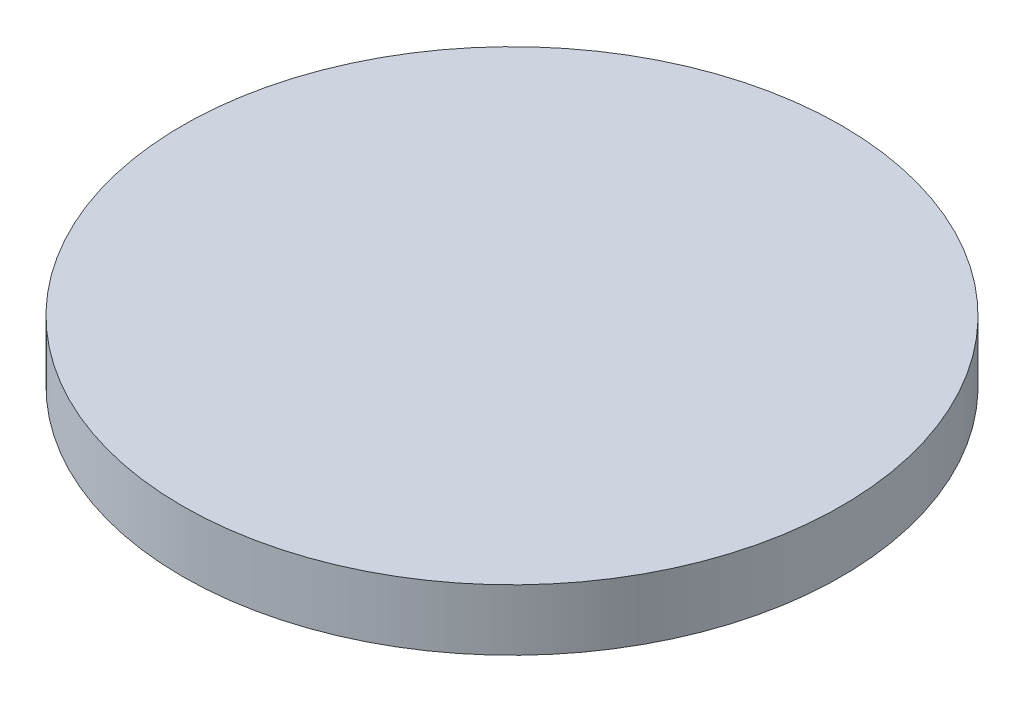
SolidWorks part; units mm, degrees
ref_plane "Front Plane" through (0, 0, 0) normal (0, 0, 1) x (1, 0, 0)
ref_plane "Top Plane" through (0, 0, 0) normal (0, 1, 0) x (1, 0, 0)
ref_plane "Right Plane" through (0, 0, 0) normal (1, 0, 0) x (0, 0, -1)
sketch "Sketch1" plane through (0, 0, 0) normal (0, 1, 0) x (1, 0, 0)
  circle A0 centre (0, 0) radius 27
  dimension "D1" = 54
extrude "Boss-Extrude1" add sketch "Sketch1" along normal blind 5
